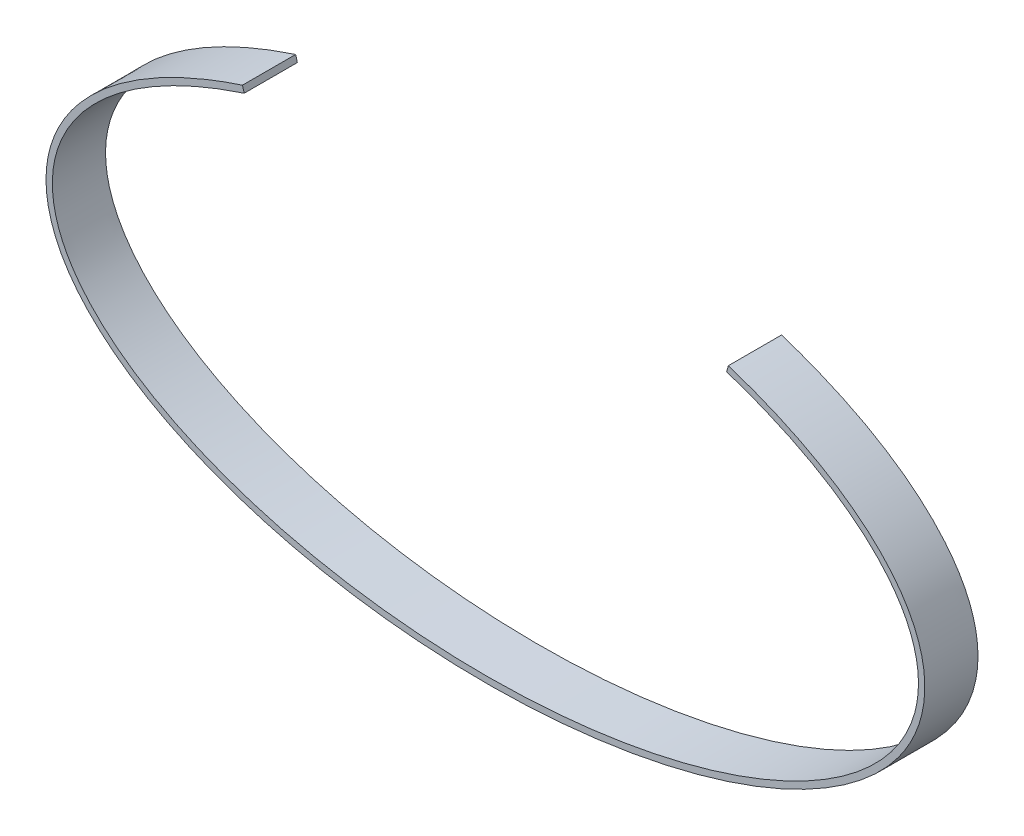
SolidWorks part; units mm, degrees
ref_plane "Front Plane" through (0, 0, 0) normal (0, 0, 1) x (1, 0, 0)
ref_plane "Top Plane" through (0, 0, 0) normal (0, 1, 0) x (1, 0, 0)
ref_plane "Right Plane" through (0, 0, 0) normal (1, 0, 0) x (0, 0, -1)
sketch "Sketch1" plane through (0, 0, 0) normal (0, 0, 1) x (1, 0, 0)
  line L0 (-22.8327, 18.6136) -> (-22.6712, 18.0351)
  line L1 (22.8327, 18.6136) -> (22.6712, 18.0351)
  spline S0 degree 3 poles (-22.8327, 18.6136) (-23.2915, 18.4644) (-23.7451, 18.3106) (-24.6349, 17.9956) (-25.072, 17.8342) (-26.3619, 17.3377) (-27.1947, 16.9898) (-29.6096, 15.8973) (-31.1043, 15.1049) (-35.1722, 12.5667) (-37.3343, 10.6572) (-39.5855, 7.5948) (-40.1712, 6.5413) (-40.9945, 4.393) (-41.2313, 3.301) (-41.3936, 0.0182) (-40.7838, -2.1885) (-38.2077, -6.3501) (-36.2388, -8.3121) (-31.1618, -11.8282) (-28.0566, -13.382) (-21.0111, -15.9318) (-17.0717, -16.9293) (-8.7552, -18.2697) (-4.3773, -18.6136) (4.3773, -18.6136) (8.7552, -18.2697) (17.0717, -16.9293) (21.0111, -15.9318) (28.0566, -13.382) (31.1618, -11.8282) (36.2388, -8.3121) (38.2077, -6.3501) (40.7838, -2.1885) (41.3936, 0.0182) (41.2313, 3.301) (40.9945, 4.393) (40.1712, 6.5413) (39.5855, 7.5948) (37.3343, 10.6572) (35.1722, 12.5667) (31.1043, 15.1049) (29.6096, 15.8973) (27.1947, 16.9898) (26.3619, 17.3377) (25.072, 17.8342) (24.6349, 17.9956) (23.7451, 18.3106) (23.2915, 18.4644) (22.8327, 18.6136) knots 0 0 0 0 0.007812 0.007812 0.015625 0.015625 0.03125 0.03125 0.0625 0.0625 0.125 0.125 0.15625 0.15625 0.1875 0.1875 0.25 0.25 0.3125 0.3125 0.375 0.375 0.4375 0.4375 0.5 0.5 0.5625 0.5625 0.625 0.625 0.6875 0.6875 0.75 0.75 0.8125 0.8125 0.84375 0.84375 0.875 0.875 0.9375 0.9375 0.96875 0.96875 0.984375 0.984375 0.992188 0.992188 1 1 1 1
  spline S1 degree 3 poles (-22.6712, 18.0351) (-23.1245, 17.8876) (-23.5734, 17.7351) (-24.4538, 17.423) (-24.8858, 17.2632) (-26.1597, 16.7722) (-26.9806, 16.4287) (-29.3596, 15.3508) (-30.8297, 14.5701) (-34.8181, 12.078) (-36.9182, 10.214) (-39.0801, 7.2675) (-39.6373, 6.2609) (-40.4148, 4.2259) (-40.6354, 3.1964) (-40.7415, 1.1323) (-40.626, 0.0977) (-40.0555, -1.9505) (-39.6009, -2.9643) (-37.7376, -5.9487) (-35.8366, -7.8603) (-30.8681, -11.3033) (-27.8064, -12.835) (-20.8401, -15.3549) (-16.9384, -16.3432) (-8.6901, -17.6723) (-4.3454, -18.0135) (4.3454, -18.0135) (8.6901, -17.6723) (16.9384, -16.3432) (20.8401, -15.3549) (27.8064, -12.835) (30.8681, -11.3033) (35.8366, -7.8603) (37.7376, -5.9487) (39.6009, -2.9643) (40.0555, -1.9505) (40.626, 0.0977) (40.7415, 1.1323) (40.6354, 3.1964) (40.4148, 4.2259) (39.6373, 6.2609) (39.0801, 7.2675) (36.9182, 10.214) (34.8181, 12.078) (30.8297, 14.5701) (29.3596, 15.3508) (26.9806, 16.4287) (26.1597, 16.7722) (24.8858, 17.2632) (24.4538, 17.423) (23.5734, 17.7351) (23.1245, 17.8876) (22.6712, 18.0351) knots 0 0 0 0 0.007813 0.007813 0.015625 0.015625 0.03125 0.03125 0.0625 0.0625 0.125 0.125 0.15625 0.15625 0.1875 0.1875 0.21875 0.21875 0.25 0.25 0.3125 0.3125 0.375 0.375 0.4375 0.4375 0.5 0.5 0.5625 0.5625 0.625 0.625 0.6875 0.6875 0.75 0.75 0.78125 0.78125 0.8125 0.8125 0.84375 0.84375 0.875 0.875 0.9375 0.9375 0.96875 0.96875 0.984375 0.984375 0.992188 0.992188 1 1 1 1
extrude "Boss-Extrude1" add sketch "Sketch1" along normal blind 5
